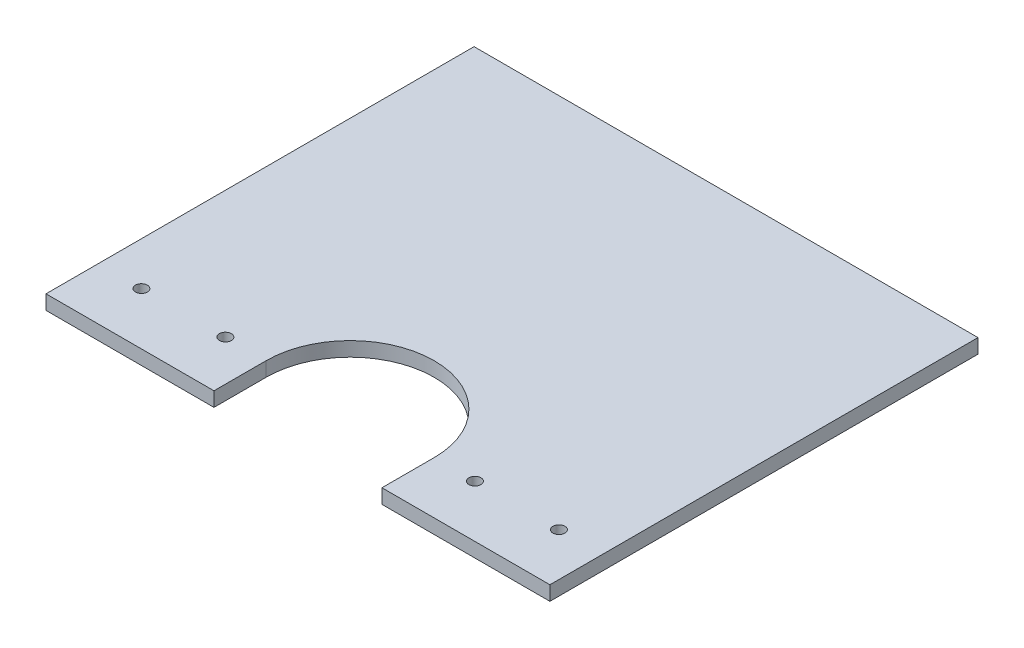
SolidWorks part; units mm, degrees
ref_plane "Front Plane" through (0, 0, 0) normal (0, 0, 1) x (1, 0, 0)
ref_plane "Top Plane" through (0, 0, 0) normal (0, 1, 0) x (1, 0, 0)
ref_plane "Right Plane" through (0, 0, 0) normal (1, 0, 0) x (0, 0, -1)
sketch "Model" plane through (0, 0, 0) normal (0, 1, 0) x (1, 0, 0)
  line L0 (-34.9972, -67.4435) -> (-34.9998, -89.2004)
  line L7 (-105.0002, 89.2004) -> (104.9997, 89.2004)
  line L8 (104.9997, 89.2004) -> (104.9997, -89.2004)
  line L9 (104.9997, -89.2004) -> (35.0002, -89.2004)
  line L10 (35.0002, -89.2004) -> (35.0028, -67.4435)
  line L12 (-34.9998, -89.2004) -> (-104.9993, -89.2004)
  line L13 (-104.9993, -89.2004) -> (-105.0002, 89.2004)
  circle A2 centre (52.0002, -67.4435) radius 2.5
  circle A4 centre (-51.9998, -67.4435) radius 2.5
  arc A5 (35.0028, -67.4435) -> (-34.9972, -67.4435) centre (0.0028, -67.4435) ccw
  circle A10 centre (-86.9998, -67.4435) radius 2.5
  circle A11 centre (87.0002, -67.4435) radius 2.5
extrude "Boss-Extrude1" add sketch "Model" along normal mid plane 6
